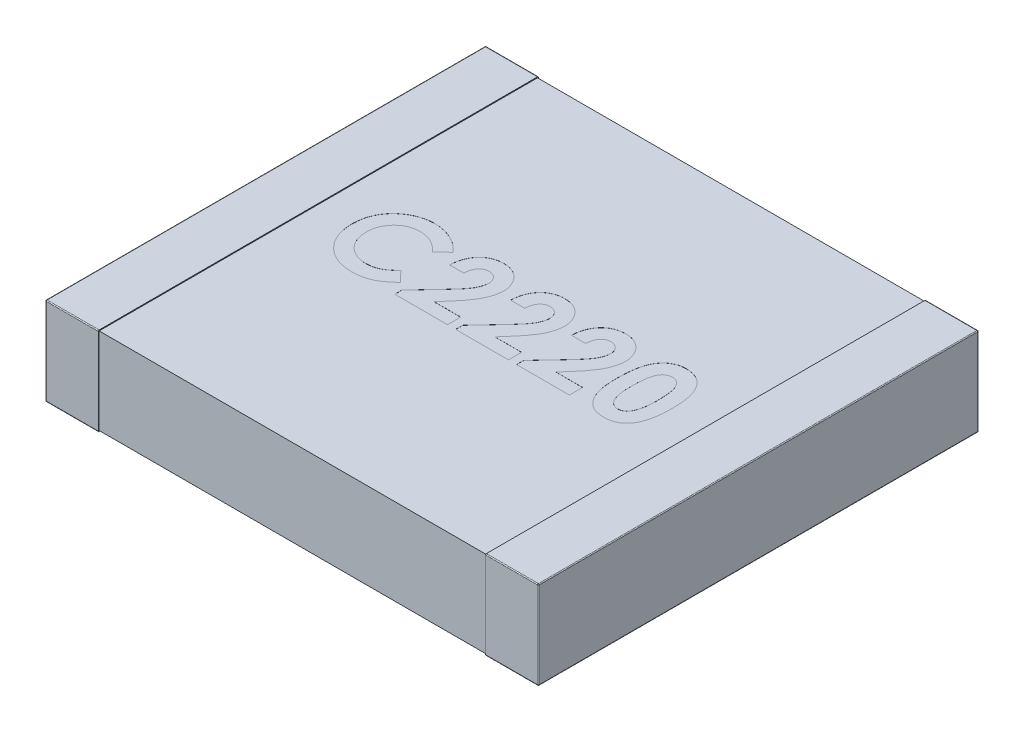
SolidWorks part; units mm, degrees
ref_plane "Front Plane" through (0, 0, 0) normal (0, 0, 1) x (1, 0, 0)
ref_plane "Top Plane" through (0, 0, 0) normal (0, 1, 0) x (1, 0, 0)
ref_plane "Right Plane" through (0, 0, 0) normal (1, 0, 0) x (0, 0, -1)
sketch "Sketch1" plane through (0, 0, 0) normal (0, 1, 0) x (1, 0, 0)
  line L0 (0, 0.15) -> (0, -0.15) construction
  line L1 (-2.8, 0) -> (0, 0) construction
  line L3 (-2.8, 2.5) -> (-2.2, 2.5)
  line L4 (-2.8, 2.5) -> (-2.8, -2.5)
  line L5 (-2.8, -2.5) -> (-2.2, -2.5)
  line L6 (-2.2, 2.5) -> (-2.2, -2.5)
  dimension "BANDWIDTH" = 0.6
  dimension "WIDTH" = 5
  dimension "LENGTH-HALF" = 2.8
extrude "THICKNESS" add sketch "Sketch1" along normal blind 1
fillet "Fillet1" radius 0.01 8 edges at (-2.8, 0, 0) (-2.5, 0, -2.5) (-2.8, 0.5, -2.5) (-2.5, 0, 2.5) (-2.8, 0.5, 2.5) (-2.8, 1, 0) (-2.5, 1, -2.5) (-2.5, 1, 2.5)
sketch "Sketch2" plane through (0, 0, 0) normal (1, 0, 0) x (0, 0, -1)
  line L0 (0, 1) -> (0, 0) construction
  line L1 (-2.49, 0.99) -> (2.49, 0.99)
  line L2 (-2.49, 0.99) -> (-2.49, 0.01)
  line L3 (-2.49, 0.01) -> (2.49, 0.01)
  line L4 (2.49, 0.99) -> (2.49, 0.01)
  line L5 (-2.49, 1) -> (2.49, 1) construction
  line L6 (-2.49, 0) -> (2.49, 0) construction
  line L7 (-2.5, 0.5) -> (2.5, 0.5) construction
  line L8 (-2.5, 0.99) -> (-2.5, 0.01) construction
  line L9 (2.5, 0.99) -> (2.5, 0.01) construction
  dimension "D1" = 0.01
  dimension "D2" = 0.01
extrude "Boss-Extrude2" add sketch "Sketch2" against normal up to surface (2.2 mm away) up to face at (-2.2, 0.5, 0)
mirror "Mirror3" about plane through (0, 0, 0) normal (1, 0, 0) of "Boss-Extrude2", "Fillet1", "THICKNESS"
sketch "Sketch3" plane through (0, 0.99, 0) normal (0, 1, 0) x (1, 0, 0)
  line L0 (-1.875, -0.45) -> (1.875, -0.45) construction
  line L1 (0, -0.55) -> (0, 0.55) construction
  line L2 (-0.55, 0) -> (0.55, 0) construction
  text T0 "<b>C2220</b>" font "Century Gothic" height 0.9
  point P2 (0, -0.45)
  dimension "D1" = 3.75
  dimension "D2" = 0.45
extrude "Cut-Extrude1" cut sketch "Sketch3" against normal blind 0.001
